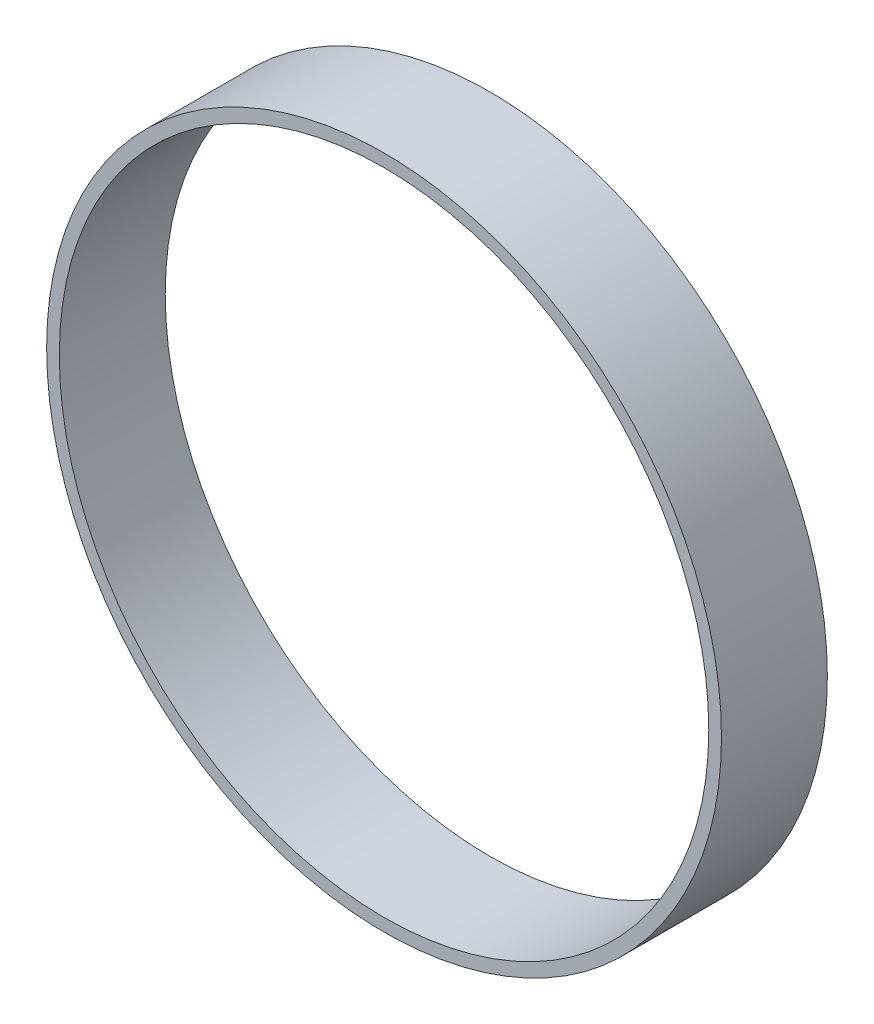
SolidWorks part; units mm, degrees
ref_plane "Alzado" through (0, 0, 0) normal (0, 0, 1) x (1, 0, 0)
ref_plane "Planta" through (0, 0, 0) normal (0, 1, 0) x (1, 0, 0)
ref_plane "Vista lateral" through (0, 0, 0) normal (1, 0, 0) x (0, 0, -1)
sketch "Croquis1" plane through (0, 0, 0) normal (0, 0, 1) x (1, 0, 0)
  circle A0 centre (-117.4611, 21.0768) radius 46
  circle A1 centre (-117.4611, 21.0768) radius 47.8
extrude "Saliente-Extruir1" add sketch "Croquis1" along normal blind 15
